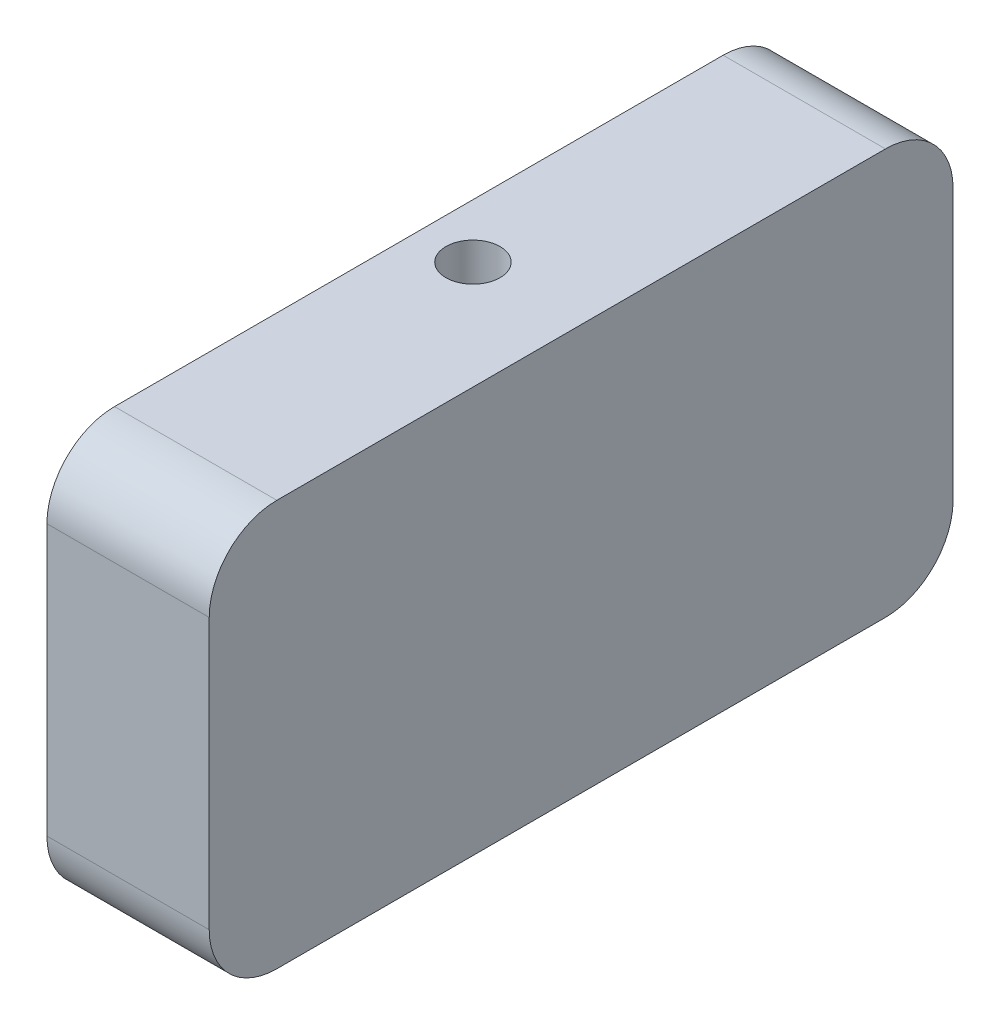
SolidWorks part; units mm, degrees
material "1060 合金"
ref_plane "前视基准面" through (0, 0, 0) normal (0, 0, 1) x (1, 0, 0)
ref_plane "上视基准面" through (0, 0, 0) normal (0, 1, 0) x (1, 0, 0)
ref_plane "右视基准面" through (0, 0, 0) normal (1, 0, 0) x (0, 0, -1)
sketch "草图1" plane through (0, 0, 0) normal (1, 0, 0) x (0, 0, -1)
  line L1 (-22.5, 15) -> (22.5, 15)
  line L2 (-27.5, 10) -> (-27.5, -10)
  line L3 (-22.5, -15) -> (22.5, -15)
  line L4 (27.5, 10) -> (27.5, -10)
  line L5 (-27.5, 15) -> (27.5, -15) construction
  line L6 (-27.5, -15) -> (27.5, 15) construction
  arc A0 (22.5, 15) -> (27.5, 10) centre (22.5, 10) cw
  arc A1 (22.5, -15) -> (27.5, -10) centre (22.5, -10) ccw
  arc A2 (-22.5, -15) -> (-27.5, -10) centre (-22.5, -10) cw
  arc A3 (-27.5, 10) -> (-22.5, 15) centre (-22.5, 10) cw
  point P0 (0, 0)
  dimension "D3" = 5
  dimension "D1" = 55
  dimension "D2" = 30
extrude "凸台-拉伸1" add sketch "草图1" along normal blind 12
sketch "草图2" plane through (0, 0, 0) normal (-1, 0, 0) x (0, 0, 1)
  circle A1 centre (0, 0) radius 8
  dimension "D1" = 16
extrude "切除-拉伸1" cut sketch "草图2" against normal blind 8 contours A1
sketch "草图3" plane through (0, -15, 0) normal (0, -1, 0) x (1, 0, 0)
  line L0 (0, 0) -> (12, 0) construction
  line L1 (12, 22.5) -> (12, -22.5) construction
  circle A0 centre (4, 0) radius 2
  dimension "D1" = 4
  dimension "D2" = 4
extrude "切除-拉伸2" cut sketch "草图3" against normal blind 40
